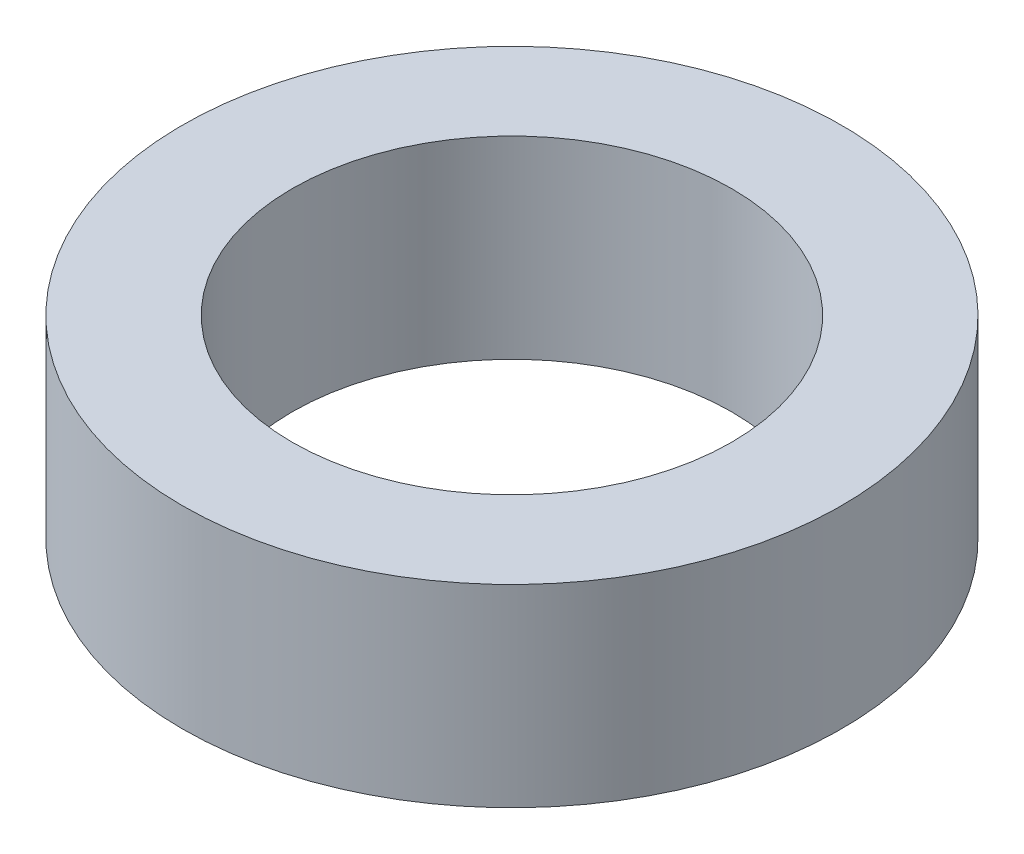
SolidWorks part; units mm, degrees
material "PVC Rigid"
ref_plane "Front Plane" through (0, 0, 0) normal (0, 0, 1) x (1, 0, 0)
ref_plane "Top Plane" through (0, 0, 0) normal (0, 1, 0) x (1, 0, 0)
ref_plane "Right Plane" through (0, 0, 0) normal (1, 0, 0) x (0, 0, -1)
sketch "Sketch1" plane through (0, 0, 0) normal (0, 1, 0) x (1, 0, 0)
  circle A0 centre (0, 0) radius 9.525
  circle A1 centre (0, 0) radius 6.35
  dimension "D1" = 19.05
  dimension "D2" = 12.7
extrude "Boss-Extrude1" add sketch "Sketch1" along normal blind 5.588
